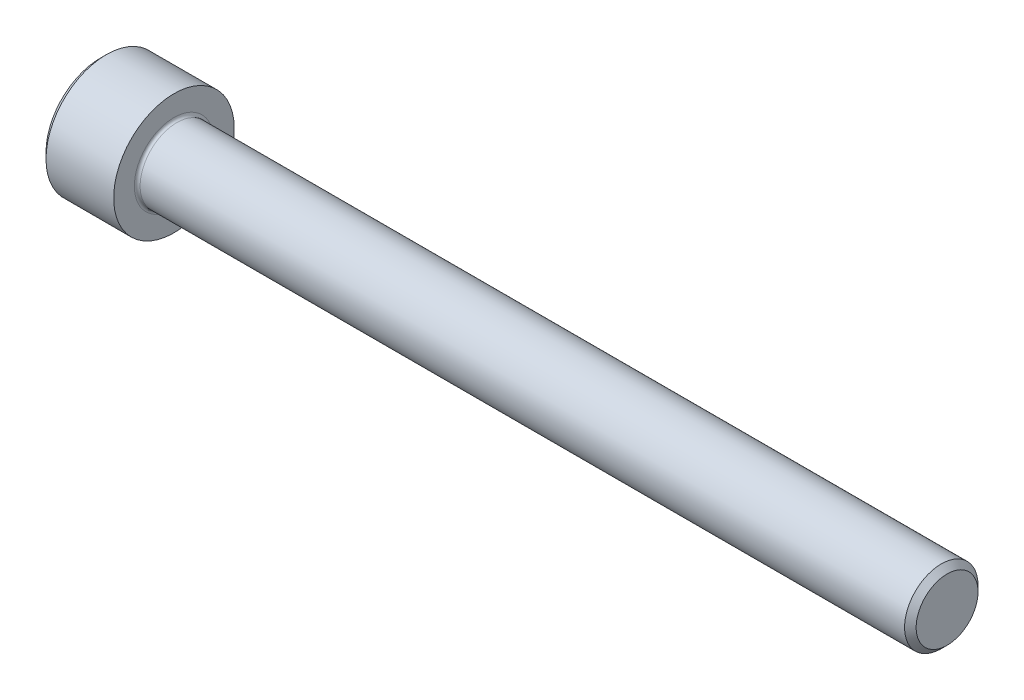
SolidWorks part; units mm, degrees
material "Alloy Steel"
ref_plane "Z Plane" through (0, 0, 0) normal (0, 0, 1) x (1, 0, 0)
ref_plane "Y Plane" through (0, 0, 0) normal (0, 1, 0) x (1, 0, 0)
ref_plane "X Plane" through (0, 0, 0) normal (1, 0, 0) x (0, 0, -1)
sketch "Sketch1" plane through (0, 0, 0) normal (0, 1, 0) x (1, 0, 0)
  line L0 (0, 3.9624) -> (0, -3.9624) construction
  line L1 (0, 0) -> (0, 3.9624)
  line L2 (0, 3.9624) -> (4.826, 3.9624)
  line L3 (4.826, 3.9624) -> (4.826, 2.413)
  line L4 (4.826, 2.413) -> (55.626, 2.413)
  line L5 (55.626, 2.413) -> (55.626, -2.413) construction
  line L6 (55.626, 2.413) -> (55.626, 0)
  line L7 (55.626, 0) -> (0, 0)
  line L8 (0, -3.9624) -> (1.6087, -3.9624) construction
  line L9 (1.6087, -3.9624) -> (3.2173, -3.9624) construction
  line L10 (3.2173, -3.9624) -> (4.826, -3.9624) construction
  point P2 (0, 0)
  point P5 (55.626, 0)
  dimension "Head Diameter" = 7.9248
  dimension "Thread Diameter" = 4.826
  dimension "Thread Length" = 50.8
revolve "Body" add sketch "Sketch1" angle 360 about L7
ref_plane "Plane1" through (3.2173, 0, 0) normal (1, 0, 0) x (0, 0, -1)
sketch "Sketch2" plane through (0, 0, 0) normal (-1, 0, 0) x (0, 0, 1)
  line L1 (-2.2914, 0) -> (-1.1457, -1.9844)
  line L2 (-1.1457, -1.9844) -> (1.1457, -1.9844)
  line L3 (1.1457, -1.9844) -> (2.2914, 0)
  line L4 (2.2914, 0) -> (1.1457, 1.9844)
  line L5 (1.1457, 1.9844) -> (-1.1457, 1.9844)
  line L6 (-1.1457, 1.9844) -> (-2.2914, 0)
  circle A0 centre (0, 0) radius 1.9844 construction
  dimension "Hex Head" = 3.9688
extrude "Hex" cut sketch "Sketch2" against normal up to surface (3.2173 mm away)
chamfer "Chamfer1" distance 0.381 angle 45 2 edges at (55.626, 0, -2.413) (0, 0, -3.9624)
fillet "Fillet1" radius 0.1905 1 edges at (4.826, 0, -2.413)
sketch "Sketch3" plane through (0, 0, 0) normal (1, 0, 0) x (0, 0, -1)
  circle A0 centre (0, 0) radius 2.2914
extrude "Hex Chamfer" cut sketch "Sketch3" along normal blind 2.54 draft 45
